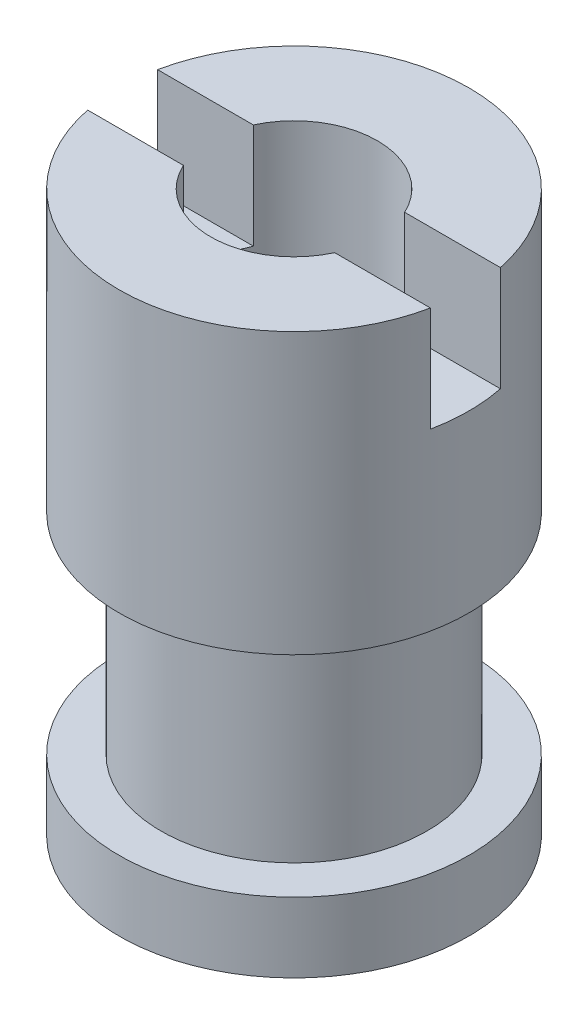
SolidWorks part; units mm, degrees
ref_plane "Front Plane" through (0, 0, 0) normal (0, 0, 1) x (1, 0, 0)
ref_plane "Top Plane" through (0, 0, 0) normal (0, 1, 0) x (1, 0, 0)
ref_plane "Right Plane" through (0, 0, 0) normal (1, 0, 0) x (0, 0, -1)
sketch "Sketch1" plane through (0, 0, 0) normal (0, 0, 1) x (1, 0, 0)
  line L1 (0, 0) -> (1.25, 0)
  line L2 (0, 0) -> (0, 4)
  line L3 (0, 4) -> (1.25, 4)
  line L4 (1.25, 2) -> (1.25, 4)
  line L5 (1.25, 0.5) -> (0.95, 0.5)
  line L6 (0.95, 0.5) -> (0.95, 2)
  line L7 (0.95, 2) -> (1.25, 2)
  line L8 (1.25, 0.5) -> (1.25, 0)
  dimension "D1" = 1.25
  dimension "D2" = 2
  dimension "D3" = 1.5
  dimension "D4" = 0.3
  dimension "D5" = 0.95
  dimension "D6" = 0.5
revolve "Revolve1" add sketch "Sketch1" angle 360 about L2
sketch "Sketch2" plane through (0, 4, 0) normal (0, 1, 0) x (1, 0, 0)
  line L0 (0, 0) -> (1.25, 0) construction
  line L1 (0, 0) -> (0, 0.25) construction
  line L2 (0, 0) -> (0, -0.25) construction
  line L3 (0, -0.25) -> (-1.5, -0.25)
  line L4 (-1.5, -0.25) -> (-1.5, 0.25)
  line L5 (-1.5, 0.25) -> (1.5, 0.25)
  line L6 (1.5, 0.25) -> (1.5, -0.25)
  line L7 (1.5, -0.25) -> (0, -0.25)
extrude "Cut-Extrude1" cut sketch "Sketch2" against normal blind 0.75
sketch "Sketch3" plane through (0, 0, 0) normal (0, -1, 0) x (1, 0, 0)
  circle A0 centre (0, 0) radius 0.5956
  dimension "D1" = 1.1913
extrude "Cut-Extrude2" cut sketch "Sketch3" against normal through all
